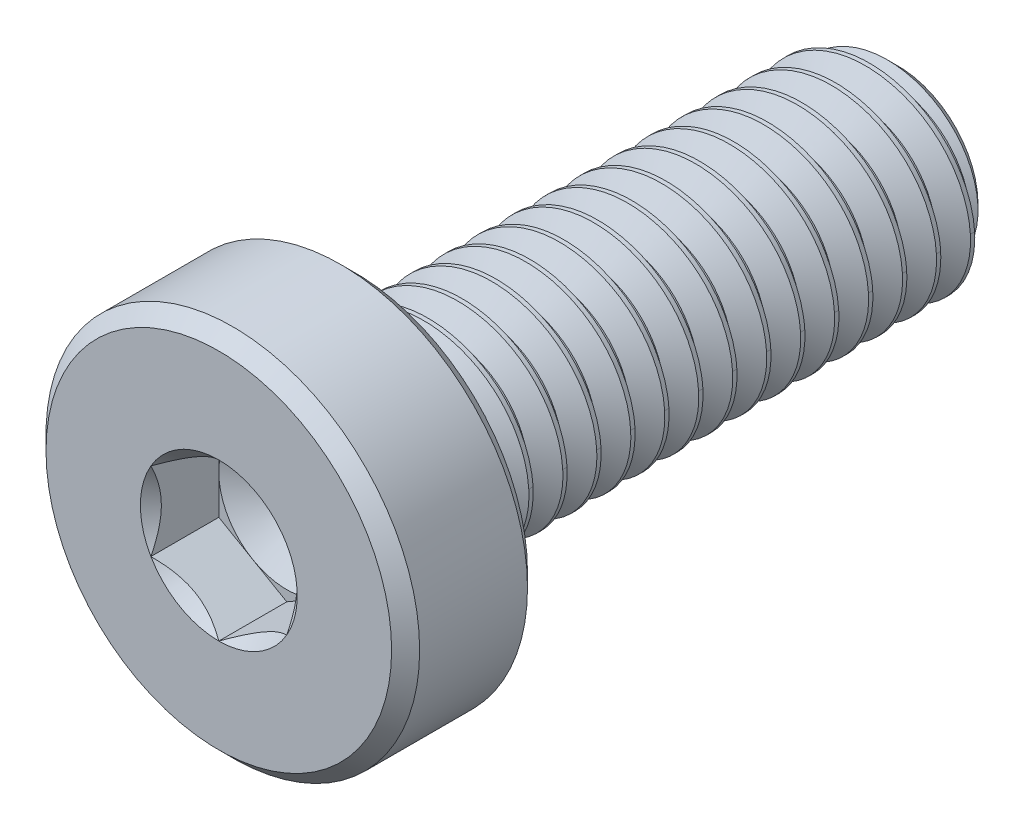
SolidWorks part; units mm, degrees
ref_plane "Front Plane" through (0, 0, 0) normal (0, 0, 1) x (1, 0, 0)
ref_plane "Top Plane" through (0, 0, 0) normal (0, 1, 0) x (1, 0, 0)
ref_plane "Right Plane" through (0, 0, 0) normal (1, 0, 0) x (0, 0, -1)
sketch "Sketch1" plane through (0, 0, 0) normal (1, 0, 0) x (0, 0, -1)
  line L0 (5, 0) -> (-5, 0) construction
  line L1 (-5, -2.75) -> (-5, 2.75) construction
  line L2 (-5, 2.75) -> (-3, 2.75) construction
  line L3 (5, -1.5) -> (5, 1.5) construction
  line L7 (4.9687, 1.5541) -> (5.4687, 1.5541) construction
  line L8 (5.4687, 1.5541) -> (5.2187, 1.1211) construction
  line L9 (5.2187, 1.1211) -> (4.9687, 1.5541) construction
  line L10 (5.2187, 1.5541) -> (5.2187, 1.5) construction
  line L11 (5.2187, 1.5) -> (5.2187, 1.1752) construction
  line L12 (5.2187, 1.1752) -> (5.2187, 1.1211) construction
  line L13 (5.1875, 1.1752) -> (5.25, 1.1752) construction
  line L14 (5, 1.5) -> (5.4375, 1.5) construction
  line L15 (4.9844, 1.5271) -> (5.4531, 1.5271) construction
  line L17 (5, -1.5) -> (3.75, -1.5) construction
  point P4 (0, 0)
  point P8 (-5, 0)
  point P11 (5, 0)
  point P16 (-5, 1)
  point P20 (5.2187, 1.1752)
  point P23 (5.2187, 1.5)
  point P26 (5.2187, 1.5271)
  point P27 (-5, -1)
  dimension "Head Diameter" = 5.5
  dimension "Head Height" = 2
  dimension "Length" = 8
  dimension "Thread Size" = 3
  dimension "Thread Pitch" = 0.5
  dimension "D1" = 0.0625
  dimension "Drive Size" = 2
  dimension "D2" = 1.25
sketch "Sketch2" plane through (0, 0, 0) normal (1, 0, 0) x (0, 0, -1)
  line L0 (-3.2063, 2.75) -> (-3, 2.5437)
  line L1 (-5, 2.75) -> (-3, 2.75) construction
  line L2 (-5, 1) -> (-4, 1)
  line L3 (-4, 1) -> (-4, 0)
  line L4 (5, 0) -> (-5, 0) construction
  line L5 (-4, 0) -> (5, 0)
  line L6 (5, 0) -> (5, 1.1752)
  line L7 (5, -1.5) -> (5, 1.5) construction
  line L8 (5, 1.1752) -> (4.6752, 1.5)
  line L9 (4.6752, 1.5) -> (-2.85, 1.5)
  line L10 (-3, 1.65) -> (-3, 2.5437)
  line L11 (-5, 1) -> (-5, 2.5437)
  line L12 (-5, -2.75) -> (-5, 2.75) construction
  line L13 (-5, 2.5437) -> (-4.7937, 2.75)
  line L14 (-4.7937, 2.75) -> (-3.2063, 2.75)
  arc A0 (-2.85, 1.5) -> (-3, 1.65) centre (-2.85, 1.65) cw
  point P24 (-3, 1.5)
  dimension "D6" = 0.15
  dimension "D1" = 45
  dimension "D3" = 1
  dimension "D4" = 45
  dimension "D5" = 0.2062
  dimension "D2" = 0.2062
revolve "Revolve1" add sketch "Sketch2" angle 360 about L5
sketch "Sketch3" plane through (0, 0, 5) normal (0, 0, 1) x (1, 0, 0)
  line L5 (0, 1.1547) -> (-1, 0.5774)
  line L7 (-1, 0.5774) -> (-1, -0.5774)
  line L8 (-1, -0.5774) -> (0, -1.1547)
  line L9 (0, -1.1547) -> (1, -0.5774)
  line L10 (1, -0.5774) -> (1, 0.5774)
  line L11 (1, 0.5774) -> (0, 1.1547)
  circle A1 centre (0, 0) radius 1 construction
  circle A2 centre (0, 0) radius 1 construction
extrude "Cut-Extrude1" cut sketch "Sketch3" against normal up to surface (1 mm away) up to face at (1, 0, 4)
sketch "Sketch4" plane through (0, 0, 5) normal (0, 0, 1) x (1, 0, 0)
  circle A0 centre (0, 0) radius 1.1547
extrude "Cut-Extrude2" cut sketch "Sketch4" against normal through all draft 45
sketch "Sketch6" plane through (0, 0, 4) normal (0, 0, 1) x (1, 0, 0)
  line L0 (-1, 0.5774) -> (-1, -0.5774) construction
  circle A1 centre (0, 0) radius 1
extrude "Cut-Extrude5" cut sketch "Sketch6" against normal through all draft 60
sketch "Sketch7" plane through (0, 0, -5) normal (0, 0, -1) x (-1, 0, 0)
  circle A0 centre (0, 0) radius 1.5
curve "Helix/Spiral1" pitch 0.5 height 8.3125 turns 16.625
sketch "Sketch8" plane through (0, 0, 0) normal (1, 0, 0) x (0, 0, -1)
  line L0 (4.9844, 1.5271) -> (5.4531, 1.5271)
  line L1 (5.4531, 1.5271) -> (5.25, 1.1752)
  line L2 (5.25, 1.1752) -> (5.1875, 1.1752)
  line L3 (5.1875, 1.1752) -> (4.9844, 1.5271)
sweep "Cut-Sweep1" cut profiles "Sketch8" path "Helix/Spiral1"
sketch "Sketch9" plane through (0, 0, 0) normal (1, 0, 0) x (0, 0, -1)
  line L0 (-3.3438, 0) -> (-3.3438, 1.65)
  line L1 (5, 0) -> (-5, 0) construction
  line L2 (-2.85, 1.5) -> (-2.5, 1.5)
  line L3 (-2.5, 1.5) -> (-1.634, 0)
  line L4 (-1.634, 0) -> (-3.3438, 0)
  line L5 (5, 1.5) -> (5.4375, 1.5) construction
  line L7 (-3, -2.5438) -> (-3, 2.5437) construction
  line L8 (-4, 0) -> (5, 0) construction
  line L9 (5, 0) -> (5, 1.1752) construction
  line L10 (-3.3438, 1.65) -> (-3, 1.65)
  arc A0 (-3, 1.65) -> (-2.85, 1.5) centre (-2.85, 1.65) ccw construction
  arc A1 (-3, 1.65) -> (-2.85, 1.5) centre (-2.85, 1.65) ccw
  dimension "D1" = 60
  dimension "D2" = 0.5
  dimension "D3" = 8.3438
revolve "Revolve2" add sketch "Sketch9" angle 360 about L4
equation "\"D1@Sketch1\"=\"Thread Pitch@Sketch1\"/8"
equation "\"D5@Sketch2\"=\"D2@Sketch2\""
equation "\"D3@Helix/Spiral1\"=\"Length@Sketch1\"+\"Thread Pitch@Sketch1\"*0.625"
equation "\"D4@Helix/Spiral1\"=\"Thread Pitch@Sketch1\""
equation "\"D2@Sketch2\"=\"Head Diameter@Sketch1\"*0.0375"
equation "\"D2@Sketch1\"=\"Thread Pitch@Sketch1\"*2.5"
equation "\"D3@Sketch2\"=\"Head Height@Sketch1\"*0.5"
equation "\"60g\"=45"
equation "\"D6@Sketch2\" = \"Thread Size@Sketch1\" * 0.05"
equation "\"D2@Sketch9\"=\"Thread Pitch@Sketch1\""
equation "\"D3@Sketch9\"=\"D3@Helix/Spiral1\"+\"D1@Sketch1\"*0.5"
